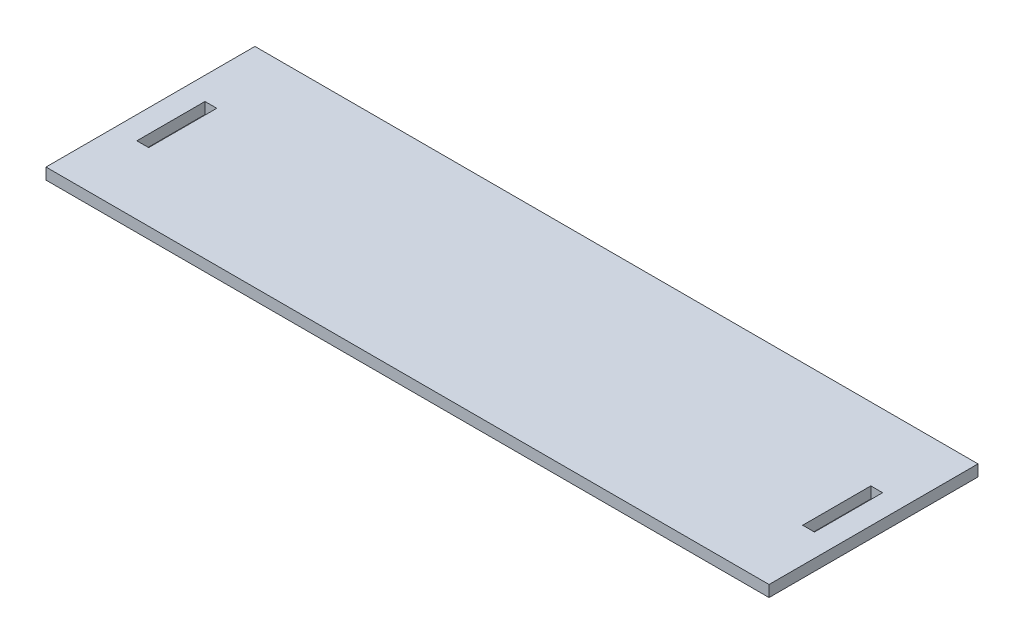
SolidWorks part; units mm, degrees
ref_plane "Front Plane" through (0, 0, 0) normal (0, 0, 1) x (1, 0, 0)
ref_plane "Top Plane" through (0, 0, 0) normal (0, 1, 0) x (1, 0, 0)
ref_plane "Right Plane" through (0, 0, 0) normal (1, 0, 0) x (0, 0, -1)
sketch "Sketch1" plane through (0, 0, 0) normal (0, 1, 0) x (1, 0, 0)
  line L0 (0, 48.236) -> (0, -48.236) construction
  line L1 (-79.6, -22.5) -> (79.6, -22.5)
  line L2 (-79.6, -22.5) -> (-79.6, 22.5)
  line L3 (-79.6, 22.5) -> (79.6, 22.5)
  line L4 (79.6, -22.5) -> (79.6, 22.5)
  line L5 (-79.6, -22.5) -> (79.6, 22.5) construction
  line L6 (-79.6, 22.5) -> (79.6, -22.5) construction
  line L7 (-74.6, -7.5) -> (-72, -7.5)
  line L8 (-74.6, -7.5) -> (-74.6, 7.5)
  line L9 (-74.6, 7.5) -> (-72, 7.5)
  line L10 (-72, -7.5) -> (-72, 7.5)
  line L11 (-74.6, -7.5) -> (-72, 7.5) construction
  line L12 (-74.6, 7.5) -> (-72, -7.5) construction
  line L13 (74.6, -7.5) -> (72, 7.5) construction
  line L14 (74.6, 7.5) -> (72, -7.5) construction
  line L15 (74.6, 7.5) -> (72, 7.5)
  line L16 (72, -7.5) -> (72, 7.5)
  line L17 (74.6, -7.5) -> (72, -7.5)
  line L18 (74.6, -7.5) -> (74.6, 7.5)
  point P0 (0, 0)
  point P6 (-73.3, 0)
  point P11 (-79.6, 0)
  point P15 (0, 0)
  dimension "D1" = 159.2
  dimension "D2" = 2.6
  dimension "D3" = 5
  dimension "D4" = 45
  dimension "D5" = 15
  dimension "D6" = 0
extrude "Boss-Extrude1" add sketch "Sketch1" along normal blind 2.5
sketch "Sketch3" plane through (0, 2.5, 0) normal (0, 1, 0) x (1, 0, 0)
  line L0 (-79.6, 22.5) -> (-79.6, 32.5)
  line L1 (-79.6, 32.5) -> (79.6, 32.5)
  line L2 (79.6, 32.5) -> (79.6, 22.5)
  line L4 (79.6, -22.5) -> (79.6, 22.5)
  line L5 (79.6, 22.5) -> (-79.6, 22.5)
  line L6 (-79.6, 22.5) -> (-79.6, -22.5)
  line L7 (-79.6, -22.5) -> (79.6, -22.5)
  line L8 (79.6, -22.5) -> (79.6, 22.5)
  line L9 (79.6, 22.5) -> (-79.6, 22.5)
  line L10 (-79.6, 22.5) -> (-79.6, -22.5)
  line L11 (-79.6, -22.5) -> (79.6, -22.5)
  line M13 (79.6, 22.5) -> (-79.6, 22.5)
  dimension "D2" = 10
  dimension "D1" = 0
extrude "Boss-Extrude3" add sketch "Sketch3" against normal blind 2.5 contours L2 L1 L0 M13
sketch "Sketch4" plane through (0, 2.5, 0) normal (0, 1, 0) x (1, 0, 0)
  line L0 (-72, 7.5) -> (-74.6, 7.5) construction
  line L1 (-74.6, -7.5) -> (-72, -7.5) construction
  line L2 (-72, -7.5) -> (-72, 7.5) construction
  line L3 (-74.6, 7.5) -> (-74.6, -7.5) construction
  line L4 (79.6, -22.5) -> (79.6, 32.5)
  line L5 (79.6, 32.5) -> (-79.6, 32.5)
  line L6 (-79.6, 32.5) -> (-79.6, -22.5)
  line L7 (-79.6, -22.5) -> (79.6, -22.5)
  line L8 (79.6, -22.5) -> (79.6, 32.5)
  line L9 (79.6, 32.5) -> (-79.6, 32.5)
  line L10 (-79.6, 32.5) -> (-79.6, -22.5)
  line L11 (-79.6, -22.5) -> (79.6, -22.5)
  line L12 (-72, 7.5) -> (-74.6, 7.5)
  line L13 (-74.6, -7.5) -> (-72, -7.5)
  line L14 (-72, -7.5) -> (-72, 7.5)
  line L15 (-74.6, 7.5) -> (-74.6, -7.5)
  line L16 (-79.6, 23.5) -> (79.6, 23.5)
  line M12 (79.6, 32.5) -> (-79.6, 32.5)
  line M13 (-79.6, 32.5) -> (-79.6, -22.5)
  dimension "D2" = 16
  dimension "D1" = 0
extrude "Cut-Extrude1" cut sketch "Sketch4" against normal through all contours L16 L8 M13 M12
